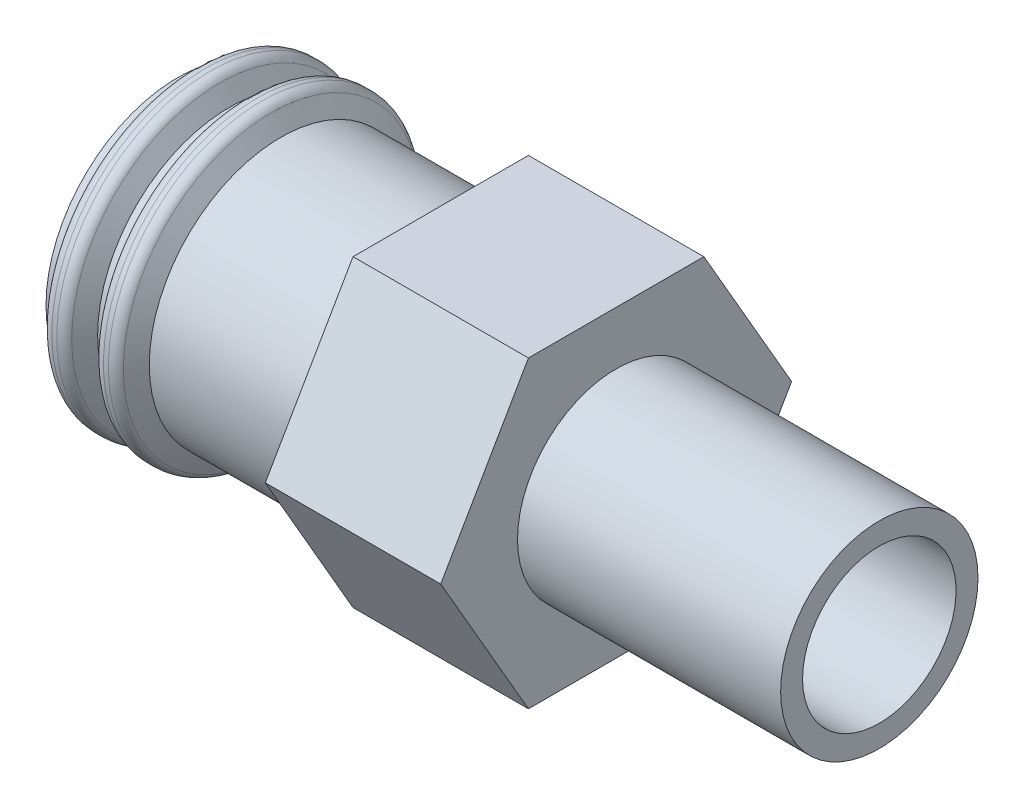
SolidWorks part; units mm, degrees
ref_plane "Plano frontal" through (0, 0, 0) normal (0, 0, 1) x (1, 0, 0)
ref_plane "Plano superior" through (0, 0, 0) normal (0, 1, 0) x (1, 0, 0)
ref_plane "Plano direito" through (0, 0, 0) normal (1, 0, 0) x (0, 0, -1)
sketch "Esboço1" plane through (0, 0, 0) normal (0, 0, 1) x (1, 0, 0)
  line L0 (-29.7219, 0) -> (34.3685, 0) construction
  line L1 (-7.3226, 3) -> (-7.1226, 3)
  line L2 (-2.5, 3) -> (-2.5, 4)
  line L3 (-2.5, 4) -> (1.5, 4)
  line L4 (1.5, 4) -> (1.5, 2.25)
  line L5 (1.5, 2.25) -> (7.5, 2.25)
  line L6 (7.5, 2.25) -> (7.5, 1.75)
  line L7 (-8.0113, 3.5) -> (-8.3, 3)
  line L8 (-8.5, 2.5) -> (-8.5, 3)
  line L9 (-4.5, 2.5) -> (-8.5, 2.5)
  line L10 (-3.201, 1.75) -> (7.5, 1.75)
  line L11 (-8.5, 2.5) -> (8.7174, 2.5) construction
  line L12 (0, 4) -> (0, 1.75) construction
  line L13 (0, 0) -> (0, 4.9732) construction
  line L14 (-4.5, 2.5) -> (-3.201, 1.75)
  line L15 (-8.0113, 3.5) -> (-7.6113, 3.5)
  line L16 (-7.6113, 3.5) -> (-7.3226, 3)
  line L17 (-7.1226, 3) -> (-6.834, 3.5)
  line L18 (-6.834, 3.5) -> (-6.434, 3.5)
  line L19 (-6.434, 3.5) -> (-6.1453, 3)
  line L20 (-6.1453, 3) -> (-2.5, 3)
  line L21 (-8.5, 3) -> (-8.3, 3)
  dimension "D12" = 60
  dimension "D1" = 5
  dimension "D2" = 4.5
  dimension "D3" = 0.5
  dimension "D4" = 16
  dimension "D5" = 8
  dimension "D6" = 6
  dimension "D7" = 4
  dimension "D8" = 4
  dimension "D9" = 6
  dimension "D10" = 7.5
  dimension "D11" = 150
  dimension "D13" = 60
  dimension "D14" = 0.5
  dimension "D15" = 0.5
  dimension "D16" = 0.4
  dimension "D17" = 0.2
  dimension "D18" = 60
  dimension "D19" = 60
  dimension "D20" = 0.5
  dimension "D21" = 0.4
  dimension "D22" = 0.2
revolve "Revolução1" add sketch "Esboço1" angle 360 about L0
sketch "Esboço2" plane through (1.5, 0, 0) normal (1, 0, 0) x (0, 0, -1)
  line L1 (4, 0) -> (2, 3.4641)
  line L2 (2, 3.4641) -> (-2, 3.4641)
  line L3 (-2, 3.4641) -> (-4, 0)
  line L4 (-4, 0) -> (-2, -3.4641)
  line L5 (-2, -3.4641) -> (2, -3.4641)
  line L6 (2, -3.4641) -> (4, 0)
  circle A0 centre (0, 0) radius 3.4641 construction
  circle A1 centre (0, 0) radius 4
  circle M2 centre (0, 0) radius 4
  dimension "D1" = 4
extrude "Corte-extrusão1" cut sketch "Esboço2" against normal blind 4 contours L2 M2 | L3 M2 | L4 M2 | L5 M2 | L6 M2 | L1 M2
fillet "Filete1" radius 0.25 2 edges at (-7.6113, 0, 3.5) (-8.0113, 0, 3.5)
fillet "Filete2" radius 0.25 2 edges at (-6.834, 0, 3.5) (-6.434, 0, 3.5)
